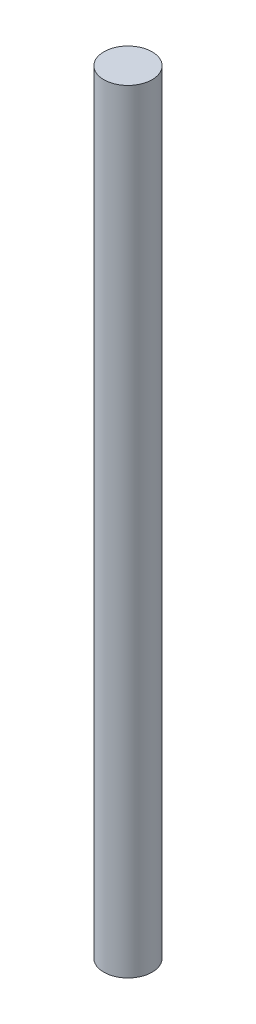
SolidWorks part; units mm, degrees
ref_plane "Front Plane" through (0, 0, 0) normal (0, 0, 1) x (1, 0, 0)
ref_plane "Top Plane" through (0, 0, 0) normal (0, 1, 0) x (1, 0, 0)
ref_plane "Right Plane" through (0, 0, 0) normal (1, 0, 0) x (0, 0, -1)
sketch "Sketch1" plane through (0, 0, 0) normal (0, 1, 0) x (1, 0, 0)
  circle A0 centre (0, 0) radius 4.7625
  dimension "D1" = 9.525
extrude "Boss-Extrude1" add sketch "Sketch1" along normal blind 152.4
